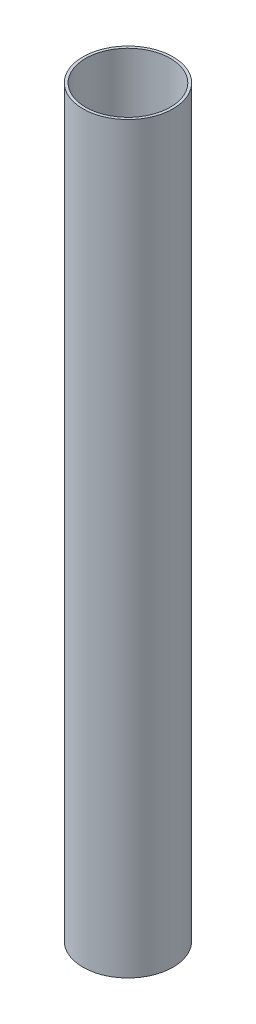
SolidWorks part; units mm, degrees
material "6063-T5"
ref_plane "Front Plane" through (0, 0, 0) normal (0, 0, 1) x (1, 0, 0)
ref_plane "Top Plane" through (0, 0, 0) normal (0, 1, 0) x (1, 0, 0)
ref_plane "Right Plane" through (0, 0, 0) normal (1, 0, 0) x (0, 0, -1)
sketch "Sketch1" plane through (0, 0, 0) normal (0, 1, 0) x (1, 0, 0)
  circle A0 centre (0, 0) radius 50
  circle A1 centre (0, 0) radius 47
  dimension "D1" = 100
  dimension "D2" = 3
extrude "Boss-Extrude1" add sketch "Sketch1" along normal blind 825
